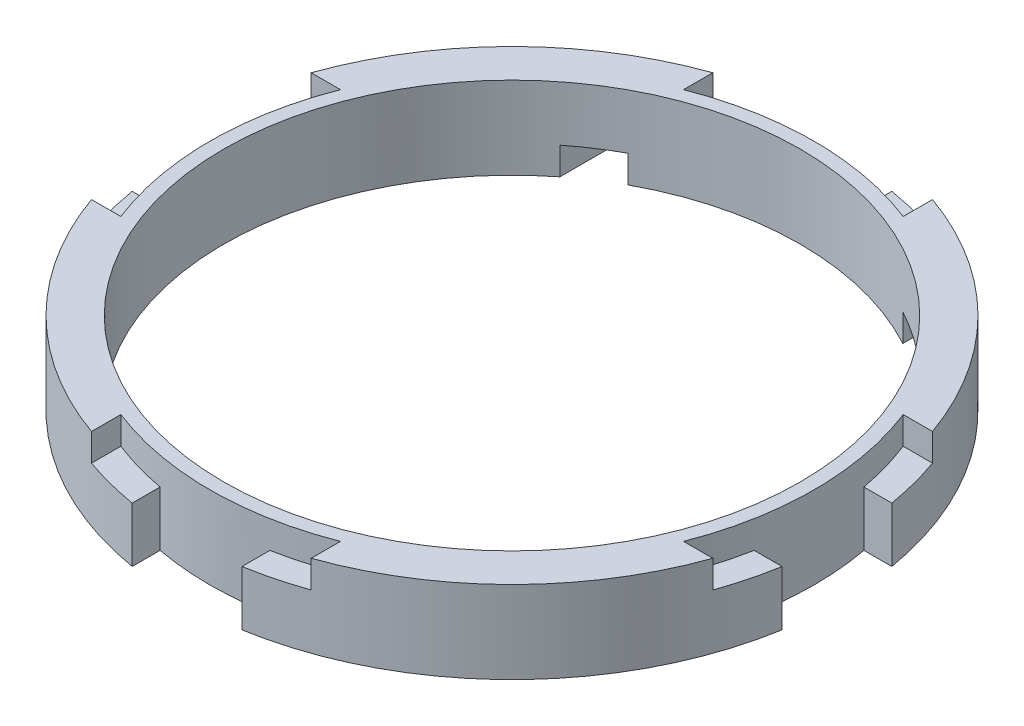
SolidWorks part; units mm, degrees
ref_plane "Front Plane" through (0, 0, 0) normal (0, 0, 1) x (1, 0, 0)
ref_plane "Top Plane" through (0, 0, 0) normal (0, 1, 0) x (1, 0, 0)
ref_plane "Right Plane" through (0, 0, 0) normal (1, 0, 0) x (0, 0, -1)
sketch "Sketch1" plane through (0, 0, 0) normal (0, 1, 0) x (1, 0, 0)
  circle A0 centre (0, 0) radius 10.5
  circle A1 centre (0, 0) radius 12
  dimension "D1" = 24
  dimension "D2" = 1.5
extrude "Boss-Extrude1" add sketch "Sketch1" against normal blind 3
ref_plane "Plane4" through (0, -2, 0) normal (0, 1, 0) x (1, 0, 0)
sketch "Sketch5" plane through (0, -2, 0) normal (0, 1, 0) x (1, 0, 0)
  line L0 (0, 0) -> (-16.6887, 0) construction
  line L1 (-11.9583, -1) -> (-12.9583, -1)
  line L2 (-11.9583, -1) -> (-11.9583, 1)
  line L3 (-11.9583, 1) -> (-12.9583, 1)
  line L4 (-12.9583, -1) -> (-12.9583, 1)
  circle A0 centre (0, 0) radius 12 construction
  dimension "D1" = 1
  dimension "D2" = 2
  dimension "D3" = 1
extrude "Boss-Extrude2" [suppressed] add sketch "Sketch5" along normal blind 2
fillet "Fillet1" [suppressed] radius 1
fillet "Fillet2" [suppressed] radius 0.25
pattern_circular "CirPattern1" [suppressed] count 4 over 360
sketch "Sketch6" plane through (0, 0, 0) normal (0, 1, 0) x (1, 0, 0)
  line L0 (0, 0) -> (0, 12) construction
  line L1 (10.247, 4) -> (11.3137, 4)
  line L2 (10.247, -4) -> (11.3137, -4)
  line L5 (-4, 10.247) -> (-4, 11.3137)
  line L6 (4, 10.247) -> (4, 11.3137)
  line L7 (4, -10.247) -> (4, -11.3137)
  line L8 (-4, -10.247) -> (-4, -11.3137)
  line L11 (-10.247, -4) -> (-11.3137, -4)
  line L12 (-10.247, 4) -> (-11.3137, 4)
  circle A0 centre (0, 0) radius 10.5 construction
  arc A1 (-4, 10.247) -> (4, 10.247) centre (0, 0) cw
  circle A4 centre (0, 0) radius 12 construction
  arc A5 (4, 11.3137) -> (-4, 11.3137) centre (0, 0) ccw
  arc A8 (11.3137, -4) -> (11.3137, 4) centre (0, 0) ccw
  arc A9 (10.247, 4) -> (10.247, -4) centre (0, 0) cw
  arc A10 (-4, -11.3137) -> (4, -11.3137) centre (0, 0) ccw
  arc A11 (4, -10.247) -> (-4, -10.247) centre (0, 0) cw
  arc A12 (-11.3137, 4) -> (-11.3137, -4) centre (0, 0) ccw
  arc A13 (-10.247, -4) -> (-10.247, 4) centre (0, 0) cw
  point P25 (0, 0)
  dimension "D1" = 0.5
  dimension "D2" = 4
  dimension "D5" = 8
extrude "Cut-Extrude1" cut sketch "Sketch6" against normal blind 1
sketch "Sketch7" plane through (0, -1, 0) normal (0, 1, 0) x (1, 0, 0)
  line L0 (-2, 10.8167) -> (-2, 11.8322)
  line L1 (2, 10.8167) -> (2, 11.8322)
  line L2 (-4, 11.3137) -> (-4, 10.247) construction
  line L3 (4, 10.247) -> (4, 11.3137) construction
  line L4 (10.8167, -2) -> (11.8322, -2)
  line L5 (10.8167, 2) -> (11.8322, 2)
  line L6 (-2, -10.8167) -> (-2, -11.8322)
  line L7 (2, -10.8167) -> (2, -11.8322)
  line L8 (-10.8167, 2) -> (-11.8322, 2)
  line L9 (-10.8167, -2) -> (-11.8322, -2)
  arc A0 (-2, 11.8322) -> (2, 11.8322) centre (0, 0) cw
  arc A1 (4, 11.3137) -> (-4, 11.3137) centre (0, 0) ccw construction
  arc A2 (-2, 10.8167) -> (2, 10.8167) centre (0, 0) cw
  arc A3 (4, 10.247) -> (-4, 10.247) centre (0, 0) ccw construction
  arc A4 (4, 10.247) -> (-4, 10.247) centre (0, 0) ccw construction
  arc A5 (11.8322, 2) -> (11.8322, -2) centre (0, 0) cw
  arc A6 (10.8167, 2) -> (10.8167, -2) centre (0, 0) cw
  arc A7 (2, -11.8322) -> (-2, -11.8322) centre (0, 0) cw
  arc A8 (2, -10.8167) -> (-2, -10.8167) centre (0, 0) cw
  arc A9 (-11.8322, -2) -> (-11.8322, 2) centre (0, 0) cw
  arc A10 (-10.8167, -2) -> (-10.8167, 2) centre (0, 0) cw
  point P34 (0, 0)
  dimension "D1" = 2
  dimension "D2" = 2
  dimension "D3" = 4
extrude "Cut-Extrude2" cut sketch "Sketch7" against normal through all
sketch "Sketch8" plane through (0, -3, 0) normal (0, -1, 0) x (1, 0, 0)
  line L0 (-5, -9.2331) -> (-5, -10.9087)
  line L1 (-6.5, -8.2462) -> (-6.5, -10.0871)
  line L2 (5, -9.2331) -> (5, -10.9087)
  line L3 (6.5, -8.2462) -> (6.5, -10.0871)
  line L4 (2, -10.8167) -> (2, -11.8322) construction
  line L5 (-2, -11.8322) -> (-2, -10.8167) construction
  circle A0 centre (0, 0) radius 10.5 construction
  arc A1 (-11.8322, -2) -> (-2, -11.8322) centre (0, 0) ccw construction
  arc A2 (2, -11.8322) -> (11.8322, -2) centre (0, 0) ccw construction
  arc A3 (-6.5, -10.0871) -> (-5, -10.9087) centre (0, 0) ccw
  arc A4 (-6.5, -8.2462) -> (-5, -9.2331) centre (0, 0) ccw
  arc A5 (5, -9.2331) -> (6.5, -8.2462) centre (0, 0) ccw
  arc A6 (5, -10.9087) -> (6.5, -10.0871) centre (0, 0) ccw
  dimension "D1" = 1.5
  dimension "D2" = 1.5
  dimension "D3" = 3
  dimension "D4" = 3
extrude "Cut-Extrude3" cut sketch "Sketch8" against normal blind 1
equation "\"dia_difflayer\"= 13"
equation "\"dia_outer_out\"= 12.5"
equation "\"dia_outer_in\"= 12"
equation "\"dia_inner_out\"= 11"
equation "\"dia_inner_in\"= 10.5"
equation "\"degrees\"= 12.5"
equation "\"d_marker\"= 1"
equation "\"t_marker\"= 0.5"
equation "\"n_markers_1\"= 6"
equation "\"n_markers_2\"= round ( 6 * sin ( 2*\"degrees\" ) / sin ( \"degrees\" ) )"
equation "\"n_markers_3\"= round ( 6 * sin ( 3*\"degrees\" ) / sin ( \"degrees\" ) )"
equation "\"n_markers_4\"= round ( 6 * sin ( 4*\"degrees\" ) / sin ( \"degrees\" ) )"
equation "\"n_markers_5\"= round ( 6 * sin ( 5*\"degrees\" ) / sin ( \"degrees\" ) )"
equation "\"n_teeth\"= 8"
equation "\"tolerance_domes\"= 0.4"
equation "\"tolerance_large\"= 0.4"
equation "\"pinhole_slot\"= 3.8"
equation "\"D1@Sketch1\"=2*\"dia_outer_in\""
